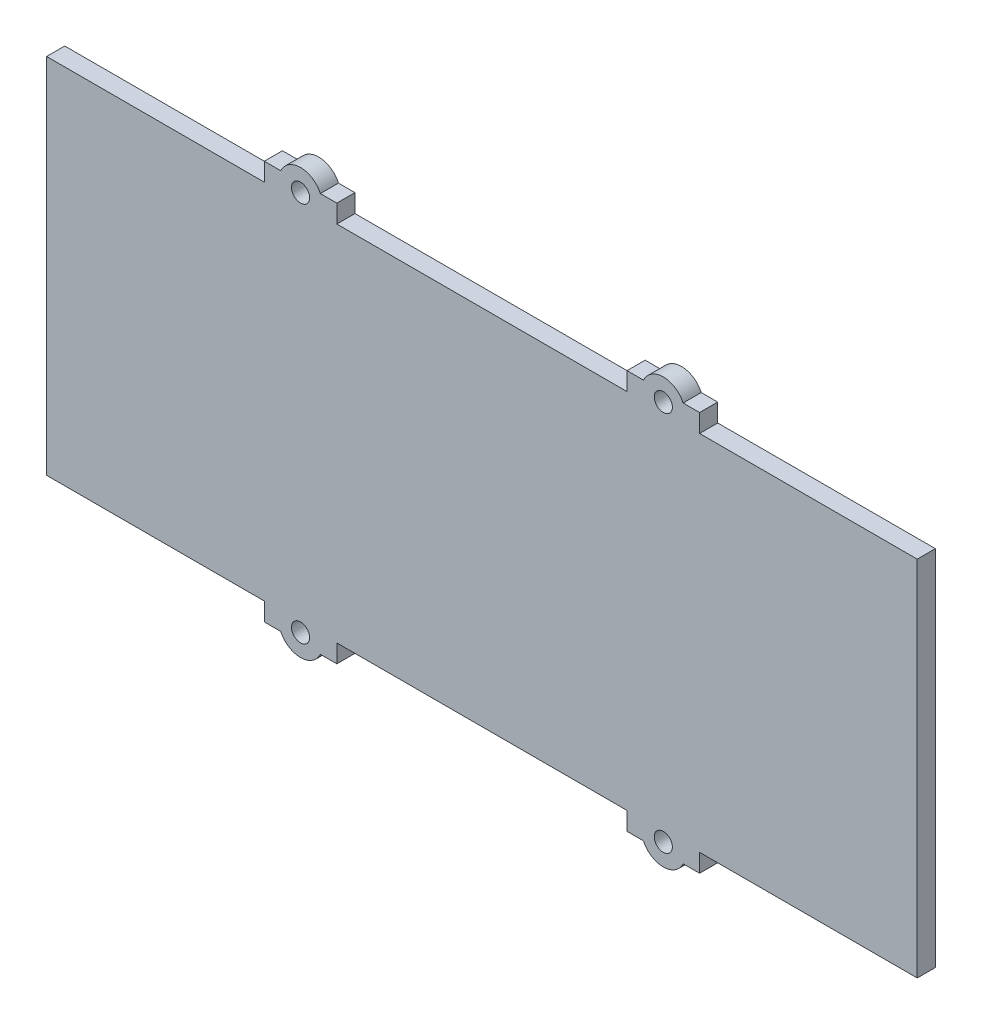
SolidWorks part; units mm, degrees
ref_plane "Front Plane" through (0, 0, 0) normal (0, 0, 1) x (1, 0, 0)
ref_plane "Top Plane" through (0, 0, 0) normal (0, 1, 0) x (1, 0, 0)
ref_plane "Right Plane" through (0, 0, 0) normal (1, 0, 0) x (0, 0, -1)
sketch "Sketch1" plane through (0, 0, 0) normal (0, 0, 1) x (1, 0, 0)
  line L1 (120, 50) -> (-120, 50)
  line L2 (120, 50) -> (120, -50)
  line L3 (120, -50) -> (-120, -50)
  line L4 (-120, 50) -> (-120, -50)
  line L5 (120, 50) -> (-120, -50) construction
  line L6 (120, -50) -> (-120, 50) construction
  point P0 (0, 0)
  dimension "D1" = 240
  dimension "D2" = 100
extrude "Boss-Extrude1" add sketch "Sketch1" along normal blind 5
sketch "Sketch2" plane through (0, 50, 0) normal (0, 1, 0) x (1, 0, 0)
  line L0 (120, 0) -> (-120, 0) construction
  line L1 (60, 0) -> (40, 0)
  line L2 (60, 0) -> (60, -5)
  line L3 (60, -5) -> (40, -5)
  line L4 (40, 0) -> (40, -5)
  line L5 (120, -5) -> (-120, -5) construction
  line L6 (120, -5) -> (120, 0) construction
  dimension "D1" = 20
  dimension "D2" = 60
  dimension "D3" = 5
extrude "Boss-Extrude2" add sketch "Sketch2" along normal blind 5
mirror "Mirror1" about plane through (0, 0, 0) normal (1, 0, 0) of "Boss-Extrude2" second plane through (0, 0, 0) second plane normal (0, 1, 0)
sketch "Sketch3" plane through (0, 0, 5) normal (0, 0, 1) x (1, 0, 0)
  line L0 (60, 55) -> (60, 50) construction
  line L1 (40, 55) -> (60, 55) construction
  line L2 (40, 50) -> (-40, 50) construction
  circle A0 centre (50, 52.5) radius 2
  circle A1 centre (50, 52.5) radius 6
  dimension "D1" = 4
  dimension "D2" = 10
  dimension "D3" = 2.5
  dimension "D4" = 2.5
  dimension "D5" = 12
extrude "Boss-Extrude3" add sketch "Sketch3" against normal blind 5
sketch "Sketch4" plane through (0, 0, 5) normal (0, 0, 1) x (1, 0, 0)
  line L0 (40, 55) -> (40, 50) construction
  line L1 (60, 55) -> (60, 50) construction
  line L2 (40, 55) -> (44.5456, 55) construction
  line L3 (40, 50) -> (-40, 50) construction
  circle A0 centre (50, 52.5) radius 2.5
  dimension "D1" = 10
  dimension "D2" = 10
  dimension "D3" = 2.5
  dimension "D4" = 2.5
  dimension "D5" = 5
extrude "Cut-Extrude2" cut sketch "Sketch4" against normal blind 5
mirror "Mirror2" about plane through (0, 0, 0) normal (0, 1, 0) of "Boss-Extrude3", "Cut-Extrude2" second plane through (0, 0, 0) second plane normal (1, 0, 0)
